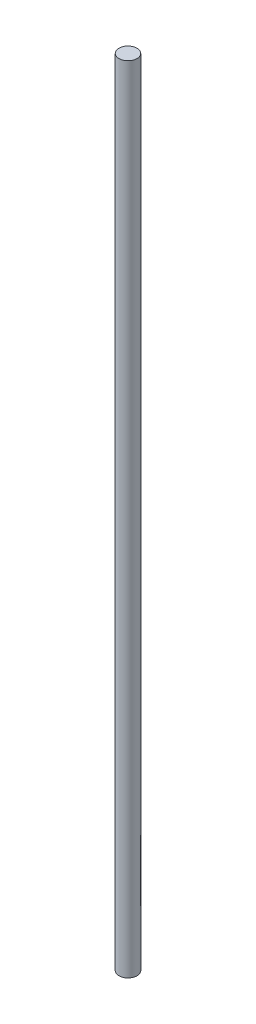
SolidWorks part; units mm, degrees
ref_plane "Front Plane" through (0, 0, 0) normal (0, 0, 1) x (1, 0, 0)
ref_plane "Top Plane" through (0, 0, 0) normal (0, 1, 0) x (1, 0, 0)
ref_plane "Right Plane" through (0, 0, 0) normal (1, 0, 0) x (0, 0, -1)
sketch "Sketch1" plane through (0, 0, 0) normal (0, 1, 0) x (1, 0, 0)
  circle A0 centre (0, 0) radius 6.35
  dimension "D1" = 12.7
extrude "Boss-Extrude1" add sketch "Sketch1" along normal blind 558.8
